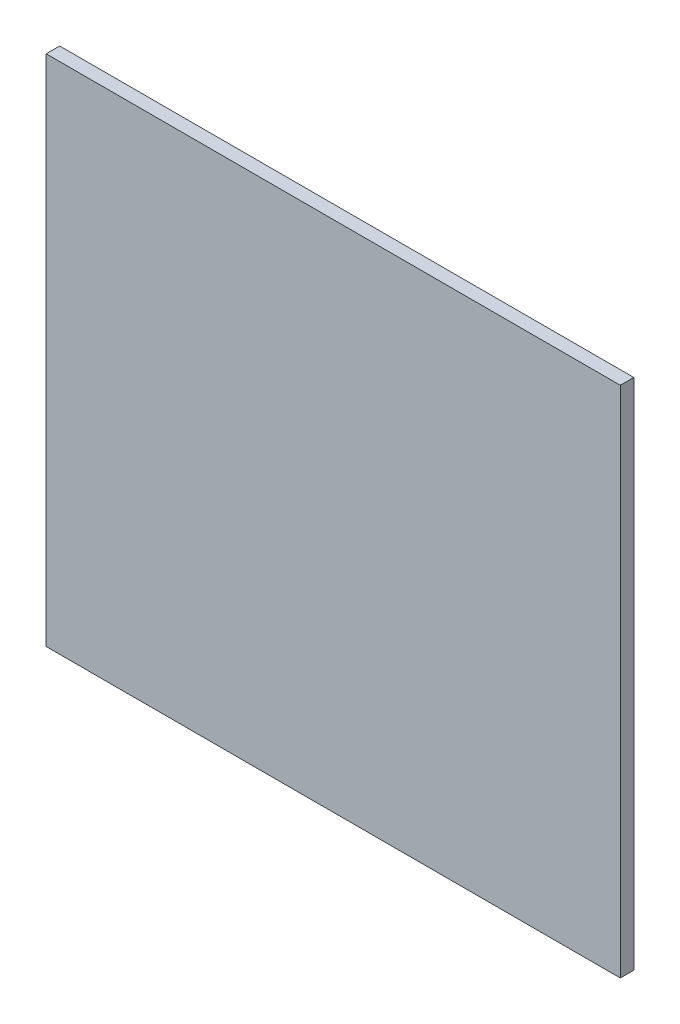
SolidWorks part; units mm, degrees
ref_plane "Front Plane" through (0, 0, 0) normal (0, 0, 1) x (1, 0, 0)
ref_plane "Top Plane" through (0, 0, 0) normal (0, 1, 0) x (1, 0, 0)
ref_plane "Right Plane" through (0, 0, 0) normal (1, 0, 0) x (0, 0, -1)
sketch "Sketch1" plane through (0, 0, 0) normal (0, 0, 1) x (1, 0, 0)
  line L1 (-212.5, 190) -> (212.5, 190)
  line L2 (-212.5, 190) -> (-212.5, -190)
  line L3 (-212.5, -190) -> (212.5, -190)
  line L4 (212.5, 190) -> (212.5, -190)
  line L5 (-212.5, 190) -> (212.5, -190) construction
  line L6 (-212.5, -190) -> (212.5, 190) construction
  point P0 (0, 0)
  dimension "D1" = 425
  dimension "D2" = 380
extrude "Boss-Extrude1" add sketch "Sketch1" along normal blind 10
